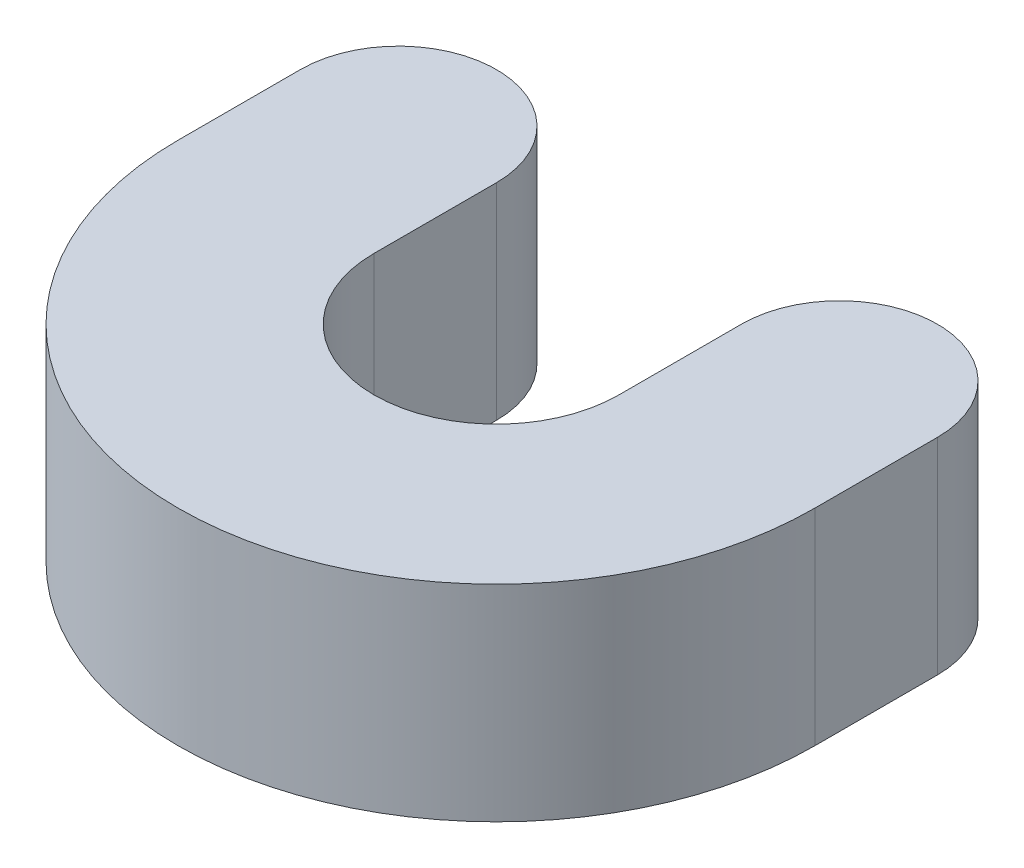
SolidWorks part; units mm, degrees
ref_plane "Спереди" through (0, 0, 0) normal (0, 0, 1) x (1, 0, 0)
ref_plane "Сверху" through (0, 0, 0) normal (0, 1, 0) x (1, 0, 0)
ref_plane "Справа" through (0, 0, 0) normal (1, 0, 0) x (0, 0, -1)
sketch "Эскиз1" plane through (0, 0, 0) normal (0, 1, 0) x (1, 0, 0)
  line L0 (-12.5, 0) -> (-12.5, 12.5) construction
  line L1 (-12.5, 12.5) -> (12.5, 12.5) construction
  line L2 (12.5, 12.5) -> (12.5, 0) construction
  line L3 (-32.5, 0) -> (-32.5, 12.5)
  line L4 (-12.5, 0) -> (-12.5, 12.5)
  line L7 (32.5, 0) -> (32.5, 12.5)
  line L9 (12.5, 0) -> (12.5, 12.5)
  circle A0 centre (0, 0) radius 12.5 construction
  arc A1 (32.5, 0) -> (-32.5, 0) centre (0, 0) cw
  arc A2 (-32.5, 12.5) -> (-12.5, 12.5) centre (-22.5, 12.5) cw
  arc A3 (12.5, 12.5) -> (32.5, 12.5) centre (22.5, 12.5) cw
  arc A4 (-12.5, 0) -> (12.5, 0) centre (0, 0) ccw
  dimension "D1" = 25
  dimension "D2" = 20
extrude "Бобышка-Вытянуть1" add sketch "Эскиз1" along normal blind 21
